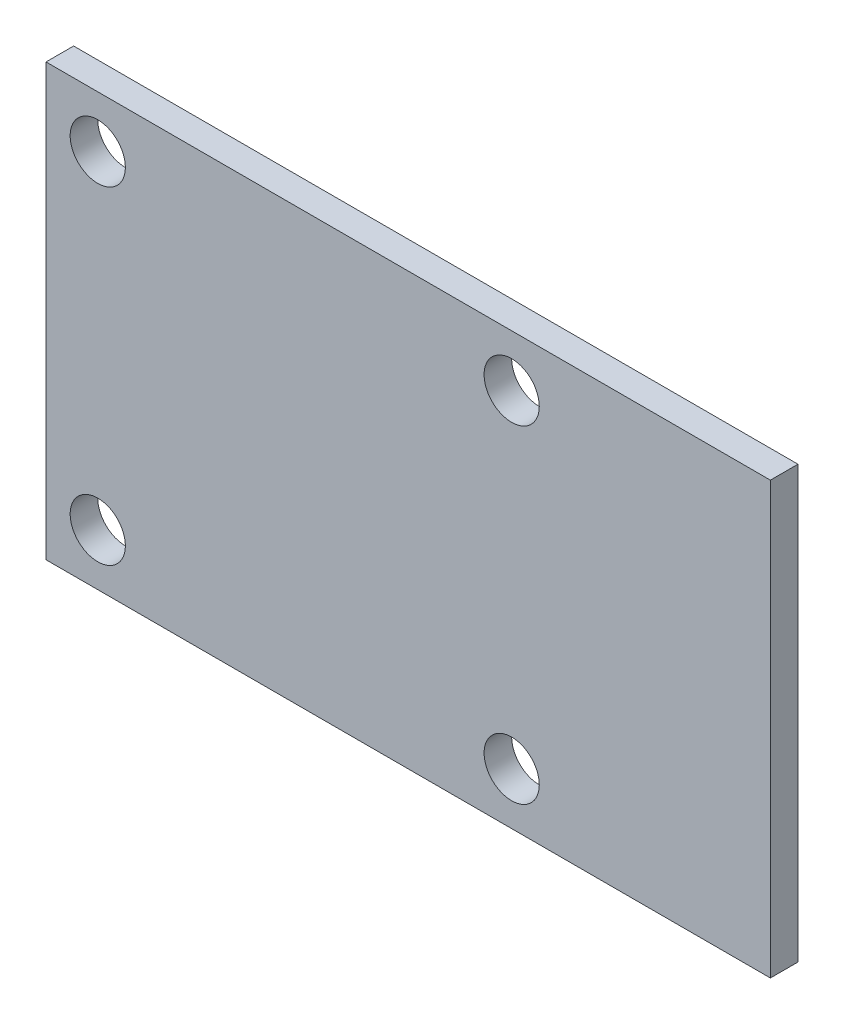
SolidWorks part; units mm, degrees
ref_plane "前视基准面" through (0, 0, 0) normal (0, 0, 1) x (1, 0, 0)
ref_plane "上视基准面" through (0, 0, 0) normal (0, 1, 0) x (1, 0, 0)
ref_plane "右视基准面" through (0, 0, 0) normal (1, 0, 0) x (0, 0, -1)
sketch "草图1" plane through (0, 0, 0) normal (0, 0, 1) x (1, 0, 0)
  line L1 (21, -12.5) -> (-21, -12.5)
  line L2 (21, -12.5) -> (21, 12.5)
  line L3 (21, 12.5) -> (-21, 12.5)
  line L4 (-21, -12.5) -> (-21, 12.5)
  line L5 (21, -12.5) -> (-21, 12.5) construction
  line L6 (21, 12.5) -> (-21, -12.5) construction
  point P0 (0, 0)
  dimension "D1" = 42
  dimension "D2" = 25
extrude "凸台-拉伸1" add sketch "草图1" along normal blind 1.6
sketch "草图2" plane through (0, 0, 1.6) normal (0, 0, 1) x (1, 0, 0)
  line L0 (-29.2902, 9.5) -> (13.4551, 9.5) construction
  line L1 (-26.7841, -9.5) -> (11.1288, -9.5) construction
  line L2 (-18, 15.6653) -> (-18, -19.87) construction
  line L3 (6, 19.9756) -> (6, -17.7446) construction
  line L4 (0, 0) -> (-30.5721, 0) construction
  line L6 (-21, 12.5) -> (-21, -12.5) construction
  circle A0 centre (-18, 9.5) radius 1.6
  circle A1 centre (-18, -9.5) radius 1.6
  circle A2 centre (6, 9.5) radius 1.6
  circle A3 centre (6, -9.5) radius 1.6
  dimension "D1" = 19
  dimension "D4" = 3.2
  dimension "D5" = 3
  dimension "D2" = 9.5
  dimension "D3" = 24
extrude "切除-拉伸1" cut sketch "草图2" against normal blind 1.6
